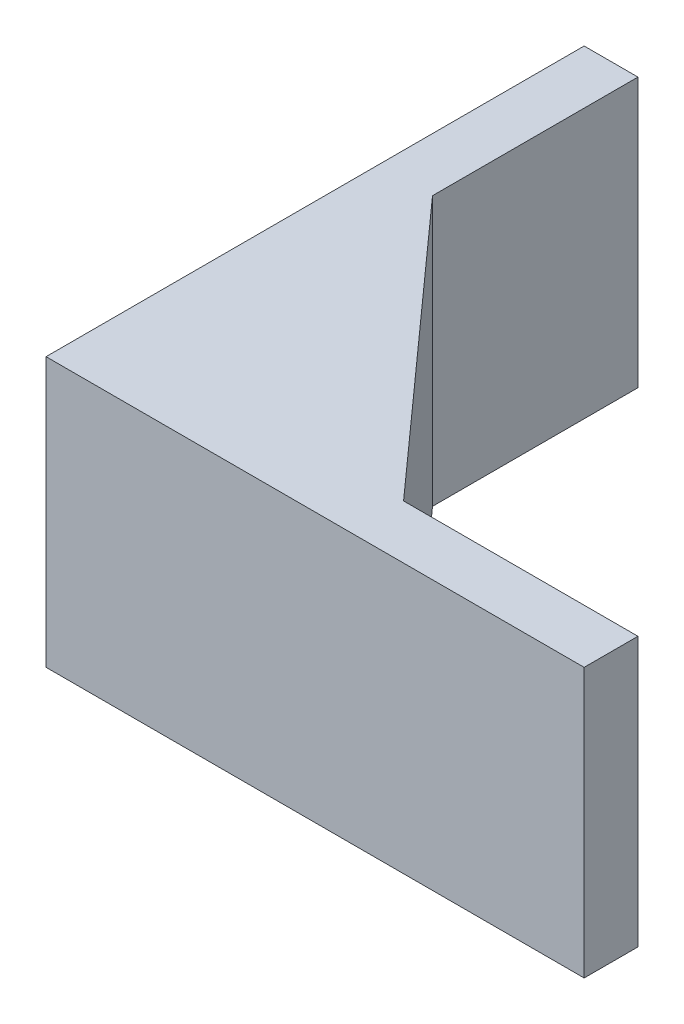
SolidWorks part; units mm, degrees
ref_plane "前视基准面" through (0, 0, 0) normal (0, 0, 1) x (1, 0, 0)
ref_plane "上视基准面" through (0, 0, 0) normal (0, 1, 0) x (1, 0, 0)
ref_plane "右视基准面" through (0, 0, 0) normal (1, 0, 0) x (0, 0, -1)
sketch "草图1" plane through (0, 0, 0) normal (0, 1, 0) x (1, 0, 0)
  line L0 (0, 40) -> (0, 0)
  line L1 (0, 0) -> (40, 0)
  line L3 (0, 40) -> (4, 40)
  line L4 (40, 0) -> (40, 4)
  line L7 (4, 24.7283) -> (22.5765, 4)
  line L8 (22.5765, 4) -> (40, 4)
  line L9 (4, 24.7283) -> (4, 40)
extrude "凸台-拉伸1" add sketch "草图1" along normal blind 20
